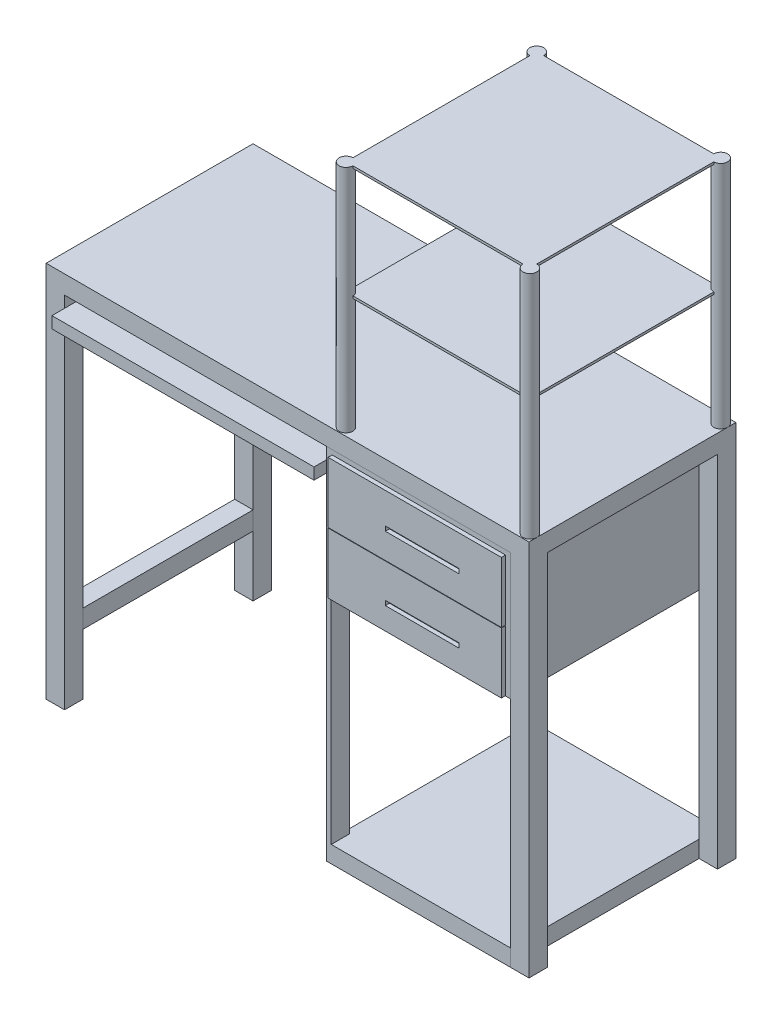
SolidWorks part; units mm, degrees
ref_plane "Front Plane" through (0, 0, 0) normal (0, 0, 1) x (1, 0, 0)
ref_plane "Top Plane" through (0, 0, 0) normal (0, 1, 0) x (1, 0, 0)
ref_plane "Right Plane" through (0, 0, 0) normal (1, 0, 0) x (0, 0, -1)
sketch "Sketch1" plane through (0, 0, 0) normal (0, 0, 1) x (1, 0, 0)
  line L0 (-1050, 0) -> (-1050, -40)
  line L1 (0, 0) -> (-1050, 0)
  line L2 (0, 0) -> (0, -40)
  line L3 (-1050, -40) -> (0, -40)
  dimension "D1" = 40
  dimension "D2" = 1050
extrude "Boss-Extrude1" add sketch "Sketch1" along normal blind 450
sketch "Sketch2" plane through (0, -40, 0) normal (0, -1, 0) x (1, 0, 0)
  line L0 (0, 450) -> (0, 0) construction
  line L1 (-1050, 450) -> (-1010, 450)
  line L2 (-1050, 450) -> (-1050, 410)
  line L3 (-1050, 410) -> (-1010, 410)
  line L4 (-1010, 450) -> (-1010, 410)
  line L5 (-1050, 0) -> (-1010, 0)
  line L6 (-1050, 0) -> (-1050, 40)
  line L7 (-1050, 40) -> (-1010, 40)
  line L8 (-1010, 0) -> (-1010, 40)
  line L9 (0, 40) -> (-40, 40)
  line L10 (0, 40) -> (0, 0)
  line L11 (0, 0) -> (-40, 0)
  line L12 (-40, 40) -> (-40, 0)
  line L13 (-1050, 0) -> (0, 0) construction
  line L15 (0, 450) -> (-40, 450)
  line L16 (0, 450) -> (0, 410)
  line L17 (0, 410) -> (-40, 410)
  line L18 (-40, 450) -> (-40, 410)
  dimension "D1" = 40
  dimension "D2" = 40
  dimension "D3" = 40
  dimension "D4" = 40
  dimension "D5" = 40
  dimension "D6" = 40
  dimension "D7" = 40
  dimension "D8" = 40
extrude "Boss-Extrude2" add sketch "Sketch2" along normal blind 781.17
sketch "Sketch3" plane through (0, 0, 450) normal (0, 0, 1) x (1, 0, 0)
  line L0 (0, -821.17) -> (-40, -821.17) construction
  line L1 (-40, -40) -> (-440, -40)
  line L2 (-40, -40) -> (-40, -821.17)
  line L3 (-40, -821.17) -> (-440, -821.17)
  line L4 (-440, -40) -> (-440, -821.17)
  dimension "D1" = 400
extrude "Boss-Extrude3" add sketch "Sketch3" against normal up to surface (450 mm away) separate body up to face at (-525, -420.585, 0)
sketch "Sketch4" plane through (0, -40, 0) normal (0, -1, 0) x (1, 0, 0)
  line L0 (-1010, 410) -> (-1010, 450) construction
  line L1 (-1010, 477.3834) -> (-440, 477.3834)
  line L2 (-1010, 477.3834) -> (-1010, 0)
  line L3 (-1010, 0) -> (-440, 0)
  line L4 (-440, 477.3834) -> (-440, 0)
extrude "Boss-Extrude4" add sketch "Sketch4" along normal blind 50 separate body
sketch "Sketch5" plane through (0, 0, 450) normal (0, 0, 1) x (1, 0, 0)
  line L0 (-427.901, -50) -> (-49.9761, -50)
  line L1 (-428.901, -50) -> (-50.9761, -50)
  line L2 (-428.901, -50) -> (-428.901, -182)
  line L3 (-428.901, -182) -> (-50.9761, -182)
  line L4 (-50.9761, -50) -> (-50.9761, -182)
  line L5 (-427.901, -50) -> (-427.901, -182)
  line L6 (-427.901, -182) -> (-49.9761, -182)
  line L7 (-49.9761, -50) -> (-49.9761, -182)
  line L8 (-427.901, -183) -> (-49.9761, -183)
  line L9 (-427.901, -183) -> (-427.901, -315)
  line L10 (-427.901, -315) -> (-49.9761, -315)
  line L11 (-49.9761, -183) -> (-49.9761, -315)
  line L12 (-427.901, -316) -> (-49.9761, -316)
  line L13 (-427.901, -316) -> (-427.901, -448)
  line L14 (-427.901, -448) -> (-49.9761, -448)
  line L15 (-49.9761, -316) -> (-49.9761, -448)
  line L16 (0, 0) -> (-1050, 0) construction
  line L28 (-428.901, -183) -> (-50.9761, -183)
  line L29 (-428.901, -183) -> (-428.901, -315)
  line L30 (-428.901, -315) -> (-50.9761, -315)
  line L31 (-50.9761, -183) -> (-50.9761, -315)
  line L32 (-428.901, -316) -> (-50.9761, -316)
  line L33 (-428.901, -316) -> (-428.901, -448)
  line L34 (-428.901, -448) -> (-50.9761, -448)
  line L35 (-50.9761, -316) -> (-50.9761, -448)
  line L48 (-143.1485, -267) -> (-303.395, -267)
  line L49 (-143.1485, -127) -> (-303.395, -127)
  line L50 (-143.1485, -127) -> (-143.1485, -117)
  line L51 (-143.1485, -117) -> (-303.395, -117)
  line L52 (-303.395, -127) -> (-303.395, -117)
  line L53 (-143.1485, -267) -> (-143.1485, -257)
  line L54 (-143.1485, -257) -> (-303.395, -257)
  line L55 (-303.395, -267) -> (-303.395, -257)
  line L56 (-143.1485, -407) -> (-303.395, -407)
  line L57 (-143.1485, -407) -> (-143.1485, -397)
  line L58 (-143.1485, -397) -> (-303.395, -397)
  line L59 (-303.395, -407) -> (-303.395, -397)
  line L72 (-427.901, -449) -> (-49.9761, -449) [skipped]
  line L73 (-427.901, -449) -> (-427.901, -581) [skipped]
  line L74 (-427.901, -581) -> (-49.9761, -581) [skipped]
  line L75 (-49.9761, -449) -> (-49.9761, -581) [skipped]
  line L76 (-427.901, -582) -> (-49.9761, -582) [skipped]
  line L77 (-427.901, -582) -> (-427.901, -714) [skipped]
  line L78 (-427.901, -714) -> (-49.9761, -714) [skipped]
  line L79 (-49.9761, -582) -> (-49.9761, -714) [skipped]
  line L80 (-427.901, -715) -> (-49.9761, -715) [skipped]
  line L81 (-427.901, -715) -> (-427.901, -847) [skipped]
  line L82 (-427.901, -847) -> (-49.9761, -847) [skipped]
  line L83 (-49.9761, -715) -> (-49.9761, -847) [skipped]
  line L84 (-428.901, -449) -> (-50.9761, -449) [skipped]
  line L85 (-428.901, -449) -> (-428.901, -581) [skipped]
  line L86 (-428.901, -581) -> (-50.9761, -581) [skipped]
  line L87 (-50.9761, -449) -> (-50.9761, -581) [skipped]
  line L88 (-428.901, -582) -> (-50.9761, -582) [skipped]
  line L89 (-428.901, -582) -> (-428.901, -714) [skipped]
  line L90 (-428.901, -714) -> (-50.9761, -714) [skipped]
  line L91 (-50.9761, -582) -> (-50.9761, -714) [skipped]
  line L92 (-428.901, -715) -> (-50.9761, -715) [skipped]
  line L93 (-428.901, -715) -> (-428.901, -847) [skipped]
  line L94 (-428.901, -847) -> (-50.9761, -847) [skipped]
  line L95 (-50.9761, -715) -> (-50.9761, -847) [skipped]
  line L96 (-143.1485, -547) -> (-303.395, -547) [skipped]
  line L97 (-143.1485, -547) -> (-143.1485, -537) [skipped]
  line L98 (-143.1485, -537) -> (-303.395, -537) [skipped]
  line L99 (-303.395, -547) -> (-303.395, -537) [skipped]
  line L100 (-143.1485, -687) -> (-303.395, -687) [skipped]
  line L101 (-143.1485, -687) -> (-143.1485, -677) [skipped]
  line L102 (-143.1485, -677) -> (-303.395, -677) [skipped]
  line L103 (-303.395, -687) -> (-303.395, -677) [skipped]
  line L104 (-143.1485, -827) -> (-303.395, -827) [skipped]
  line L105 (-143.1485, -827) -> (-143.1485, -817) [skipped]
  line L106 (-143.1485, -817) -> (-303.395, -817) [skipped]
  line L107 (-303.395, -827) -> (-303.395, -817) [skipped]
  dimension "D4" = 132
  dimension "D5" = 1
  dimension "D6" = 50
  dimension "D7" = 10
  dimension "D8" = 67
  dimension "D2" = 2
  dimension "D1" = 6
  dimension "D3" = 6
extrude "Boss-Extrude5" add sketch "Sketch5" along normal blind 9 separate body contours L35 L12 L13 L14 L56 L59 L58 L57 | L31 L8 L9 L10 L48 L55 L54 L53 | L0 L5 L3 L4 L49 L52 L51 L50
sketch "Sketch6" plane through (0, 0, 450) normal (0, 0, 1) x (1, 0, 0)
  line L1 (-430, -315.5912) -> (-40, -315.5912)
  line L2 (-430, -315.5912) -> (-430, -784.6411)
  line L3 (-430, -784.6411) -> (-40, -784.6411)
  line L4 (-40, -315.5912) -> (-40, -784.6411)
  line L5 (0, -821.17) -> (0, 0) construction
  line L6 (-440, -40) -> (-440, -821.17) construction
  dimension "D1" = 40
  dimension "D2" = 10
extrude "Cut-Extrude1" cut sketch "Sketch6" against normal through all and the other way blind 358
sketch "Sketch7" plane through (-430, 0, 0) normal (1, 0, 0) x (0, 0, -1)
  line L0 (-410, -821.17) -> (-410, -40) construction
  line L1 (-410, -784.6411) -> (-40, -784.6411)
  line L2 (-410, -784.6411) -> (-410, -314.6411)
  line L3 (-410, -314.6411) -> (-40, -314.6411)
  line L4 (-40, -784.6411) -> (-40, -314.6411)
  line L5 (0, -784.6411) -> (-450, -784.6411) construction
extrude "Cut-Extrude2" cut sketch "Sketch7" against normal blind 10
sketch "Sketch8" plane through (0, 0, 40) normal (0, 0, 1) x (1, 0, 0)
  line L0 (-1050, -821.17) -> (-1050, -40) construction
  line L1 (-1050, -689.535) -> (-1010, -689.535)
  line L2 (-1050, -689.535) -> (-1050, -649.535)
  line L3 (-1050, -649.535) -> (-1010, -649.535)
  line L4 (-1010, -689.535) -> (-1010, -649.535)
  line L5 (-1010, -821.17) -> (-1010, -40) construction
  dimension "D1" = 40
extrude "Boss-Extrude6" add sketch "Sketch8" along normal up to surface (370 mm away) up to face at (-1035, -528.2312, 410)
sketch "Sketch9" plane through (0, 0, 477.3834) normal (0, 0, 1) x (1, 0, 0)
  line L0 (-440, -90) -> (-440, -40) construction
  line L1 (-1010, -40) -> (-440, -40)
  line L2 (-1010, -40) -> (-1010, -65)
  line L3 (-1010, -65) -> (-440, -65)
  line L4 (-440, -40) -> (-440, -65)
extrude "Cut-Extrude3" cut sketch "Sketch9" against normal through all
sketch "Sketch10" plane through (0, 0, 0) normal (0, 1, 0) x (1, 0, 0)
  line L0 (0, -450) -> (0, 0) construction
  circle A0 centre (-15, -432.9023) radius 15
  circle A1 centre (-15, -18.0331) radius 15
  circle A2 centre (-415, -432.9023) radius 15
  circle A3 centre (-415, -18.0331) radius 15
  dimension "D1" = 30
  dimension "D2" = 400
  dimension "D3" = 400
extrude "Boss-Extrude7" add sketch "Sketch10" along normal blind 500
sketch "Sketch11" plane through (0, 500, 0) normal (0, 1, 0) x (1, 0, 0)
  line L1 (-415, -432.9023) -> (-15, -432.9023)
  line L2 (-415, -432.9023) -> (-415, -18.0331)
  line L3 (-415, -18.0331) -> (-15, -18.0331)
  line L4 (-15, -432.9023) -> (-15, -18.0331)
extrude "Boss-Extrude8" add sketch "Sketch11" against normal blind 5
ref_plane "Plane1" through (0, 250, 0) normal (0, 1, 0) x (1, 0, 0)
sketch "Sketch12" plane through (0, 250, 0) normal (0, 1, 0) x (1, 0, 0)
  line L0 (-30, -18.0331) -> (-400, -18.0331) construction
  line L1 (-15, -432.9023) -> (-415.4249, -432.9023)
  line L2 (-15, -432.9023) -> (-15, -18.0331)
  line L3 (-15, -18.0331) -> (-415.4249, -18.0331)
  line L4 (-415.4249, -432.9023) -> (-415.4249, -18.0331)
extrude "Boss-Extrude9" add sketch "Sketch12" along normal blind 5
equation "\"D2\"=30"
equation "\"D1@Sketch10\"=\"D2\""
